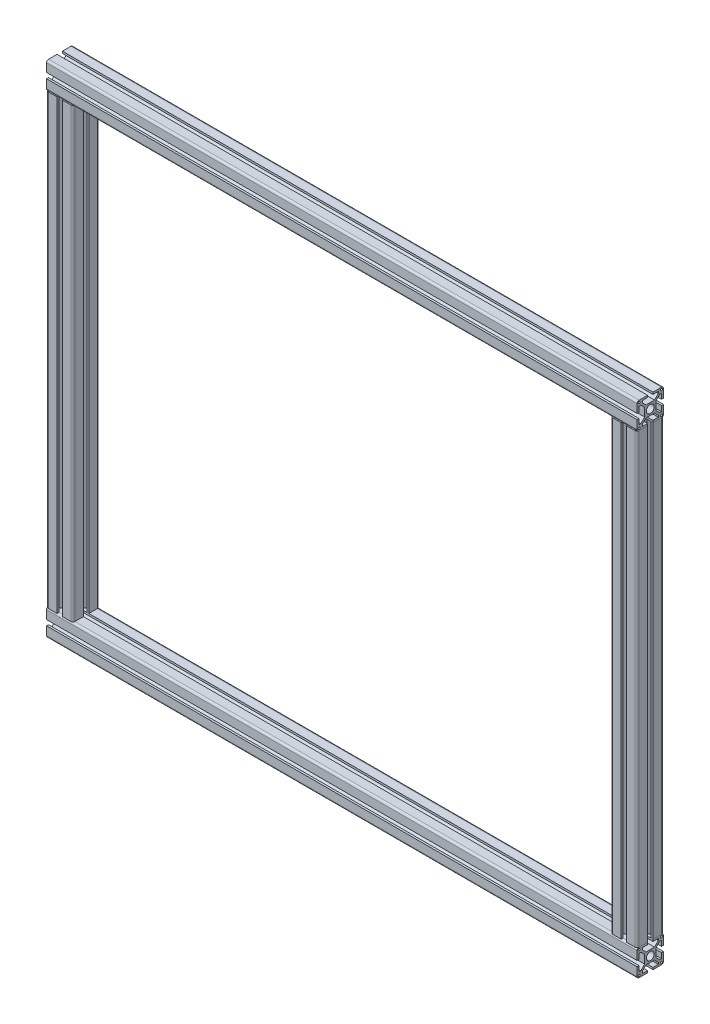
SolidWorks part; units mm, degrees
material "6061-T6 (SS)"
ref_plane "Front Plane" through (0, 0, 0) normal (0, 0, 1) x (1, 0, 0)
ref_plane "Top Plane" through (0, 0, 0) normal (0, 1, 0) x (1, 0, 0)
ref_plane "Right Plane" through (0, 0, 0) normal (1, 0, 0) x (0, 0, -1)
sketch3d "3DSketch1"
  line L0 (0, 0, 0) -> (855, 0, 0)
  line L1 (855, 0, 0) -> (855, 718, 0)
  line L2 (855, 718, 0) -> (0, 718, 0)
  line L3 (0, 718, 0) -> (0, 0, 0)
  dimension "D1" = 855
  dimension "D2" = 718
other "4040 4040_ALEX(1)"
ref_plane "Plane3" through (855, 718, 0) normal (-1, 0, 0) x (0, 0, 1)
sketch "Sketch1" plane through (855, 718, 0) normal (-1, 0, 0) x (0, 0, 1)
  line L0 (0, 20) -> (0, -20) construction
  line L1 (20, 0) -> (-20, 0) construction
  line L2 (6.3787, 8.5) -> (-6.3787, 8.5)
  line L3 (-6.3787, 8.5) -> (-12.1287, 14.25)
  line L4 (-12.1287, 14.25) -> (-12.1287, 17)
  line L5 (-12.1287, 17) -> (-4.1, 17)
  line L6 (-4.1, 17) -> (-4.1, 20)
  line L7 (-4.1, 20) -> (-17, 20)
  line L8 (-20, 17) -> (-20, 4.1)
  line L9 (-20, 4.1) -> (-17, 4.1)
  line L10 (-17, 4.1) -> (-17, 12.1287)
  line L11 (-17, 12.1287) -> (-14.25, 12.1287)
  line L12 (-14.25, 12.1287) -> (-8.5, 6.3787)
  line L13 (-8.5, 6.3787) -> (-8.5, -6.3787)
  line L14 (0, 0) -> (-17, 17) construction
  line L15 (8.5, 6.3787) -> (8.5, -6.3787)
  line L16 (6.3787, 8.5) -> (12.1287, 14.25)
  line L17 (14.25, 12.1287) -> (8.5, 6.3787)
  line L18 (20, 4.1) -> (17, 4.1)
  line L19 (17, 4.1) -> (17, 12.1287)
  line L20 (17, 12.1287) -> (14.25, 12.1287)
  line L21 (12.1287, 14.25) -> (12.1287, 17)
  line L22 (4.1, 17) -> (4.1, 20)
  line L23 (12.1287, 17) -> (4.1, 17)
  line L24 (4.1, 20) -> (17, 20)
  line L25 (20, 17) -> (20, 4.1)
  line L26 (0, 0) -> (17, 17) construction
  line L27 (-8.5, 6.3787) -> (-6.3787, 8.5) construction
  line L28 (20, -4.1) -> (17, -4.1)
  line L29 (17, -12.1287) -> (14.25, -12.1287)
  line L30 (17, -4.1) -> (17, -12.1287)
  line L31 (20, -17) -> (20, -4.1)
  line L32 (4.1, -20) -> (17, -20)
  line L33 (4.1, -17) -> (4.1, -20)
  line L34 (12.1287, -17) -> (4.1, -17)
  line L35 (12.1287, -14.25) -> (12.1287, -17)
  line L36 (6.3787, -8.5) -> (12.1287, -14.25)
  line L37 (14.25, -12.1287) -> (8.5, -6.3787)
  line L38 (-6.3787, -8.5) -> (-12.1287, -14.25)
  line L39 (6.3787, -8.5) -> (-6.3787, -8.5)
  line L40 (-14.25, -12.1287) -> (-8.5, -6.3787)
  line L41 (-20, -4.1) -> (-17, -4.1)
  line L42 (-17, -4.1) -> (-17, -12.1287)
  line L43 (-17, -12.1287) -> (-14.25, -12.1287)
  line L44 (-4.1, -17) -> (-4.1, -20)
  line L45 (-12.1287, -14.25) -> (-12.1287, -17)
  line L46 (-12.1287, -17) -> (-4.1, -17)
  line L47 (-4.1, -20) -> (-17, -20)
  line L48 (-20, -17) -> (-20, -4.1)
  circle A0 centre (0, 0) radius 6
  arc A1 (-17, 20) -> (-20, 17) centre (-17, 17) ccw
  circle A2 centre (-17, 17) radius 1.5
  arc A3 (17, 20) -> (20, 17) centre (17, 17) cw
  circle A4 centre (17, 17) radius 1.5
  circle A5 centre (17, -17) radius 1.5
  arc A6 (17, -20) -> (20, -17) centre (17, -17) ccw
  arc A7 (-17, -20) -> (-20, -17) centre (-17, -17) cw
  circle A8 centre (-17, -17) radius 1.5
  point P5 (0, 0)
  point P9 (0, 0)
  point P27 (0, 8.5)
  point P54 (8.5, 0)
  point P55 (-8.5, 0)
  point P68 (-20, -20)
  point P69 (0, 0)
  point P70 (20, 0)
  point P71 (0, -20)
  point P72 (-20, 0)
  point P73 (0, 20)
  point P74 (0, 0)
  point P75 (-20, 20)
  point P76 (20, 20)
  point P77 (20, -20)
  point P78 (0, 0)
  dimension "D1" = 12
  dimension "D7" = 3
  dimension "D8" = 3
  dimension "D2" = 40
  dimension "D3" = 45
  dimension "D4" = 11.5
  dimension "D5" = 4.1
  dimension "D6" = 3
  dimension "D9" = 5.75
  dimension "D10" = 3
equation "\"W\"= 1750"
equation "\"L\"= 780"
equation "\"H\"= 780"
equation "\"ARM_BOLT_SPACING\"= 166"
equation "\"ARM_TO_WALL\"= 200"
equation "\"D1@3DSketch1\"=(\"W\"/2)-20"
equation "\"D2@3DSketch1\"=\"H\"-62"
